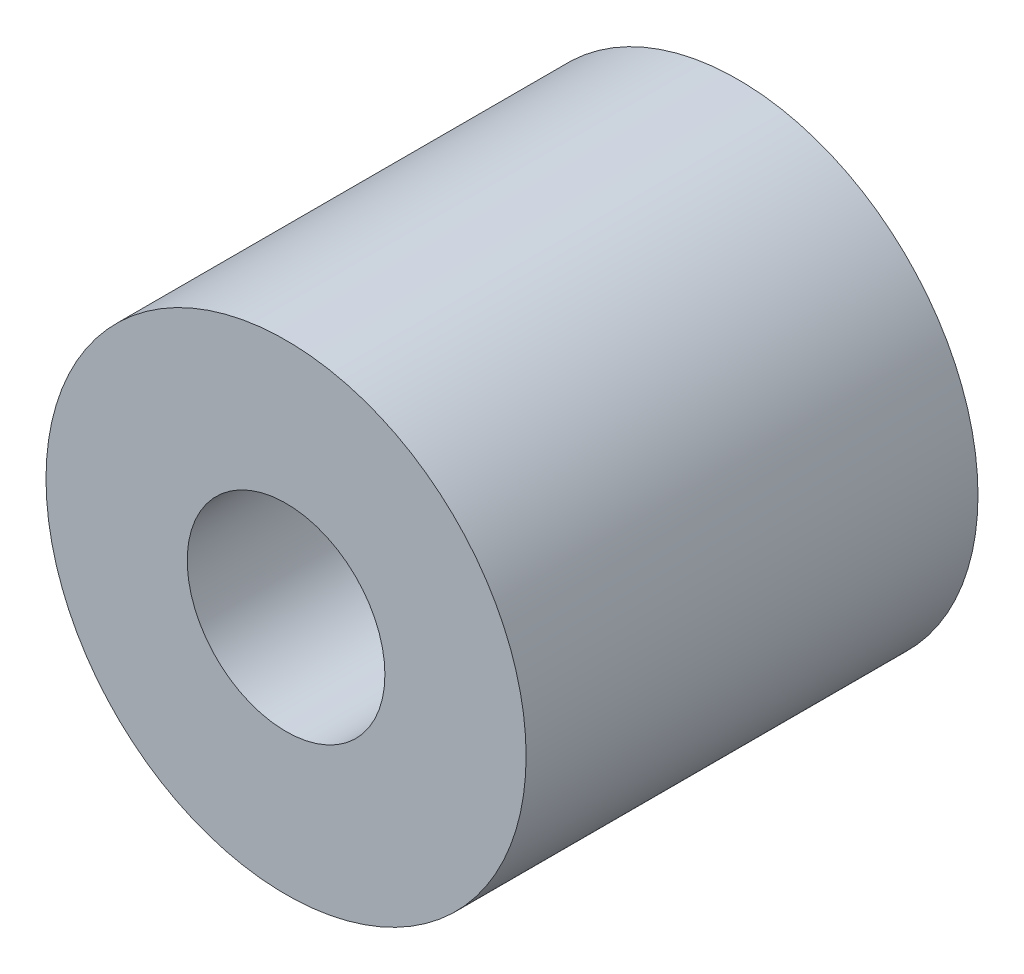
SolidWorks part; units mm, degrees
ref_plane "Front Plane" through (0, 0, 0) normal (0, 0, 1) x (1, 0, 0)
ref_plane "Top Plane" through (0, 0, 0) normal (0, 1, 0) x (1, 0, 0)
ref_plane "Right Plane" through (0, 0, 0) normal (1, 0, 0) x (0, 0, -1)
sketch "Sketch1" plane through (0, 0, 0) normal (0, 0, 1) x (1, 0, 0)
  circle A0 centre (0, 0) radius 3.5
  circle A1 centre (0, 0) radius 8.5
  dimension "D1" = 7
  dimension "D2" = 17
extrude "Boss-Extrude1" add sketch "Sketch1" along normal blind 16
